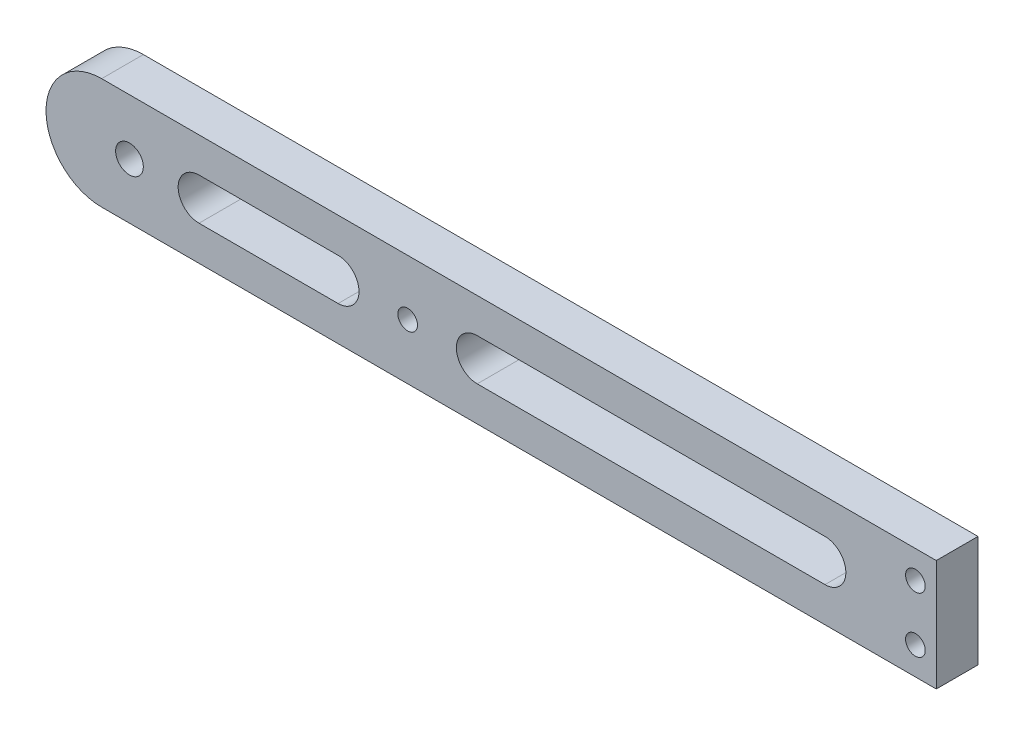
SolidWorks part; units mm, degrees
material "6061-T6 (SS)"
ref_plane "Front Plane" through (0, 0, 0) normal (0, 0, 1) x (1, 0, 0)
ref_plane "Top Plane" through (0, 0, 0) normal (0, 1, 0) x (1, 0, 0)
ref_plane "Right Plane" through (0, 0, 0) normal (1, 0, 0) x (0, 0, -1)
sketch "Sketch1" plane through (0, 0, 0) normal (0, 0, 1) x (1, 0, 0)
  line L1 (0, 0) -> (-203.2, 0)
  line L2 (0, 0) -> (0, 25.4)
  line L3 (0, 25.4) -> (-203.2, 25.4)
  line L4 (-203.2, 0) -> (-203.2, 25.4)
  dimension "D1" = 25.4
  dimension "D2" = 203.2
extrude "Boss-Extrude1" add sketch "Sketch1" along normal blind 9.525
sketch "Sketch2" plane through (0, 0, 9.525) normal (0, 0, 1) x (1, 0, 0)
  line L0 (-4.7625, 6.35) -> (-4.7625, 19.05)
  line L1 (-4.7625, 19.05) -> (-4.7625, 25.4)
  line L2 (0, 25.4) -> (-203.2, 25.4) construction
  line L3 (-4.7625, 6.35) -> (-4.7625, 0)
  line L4 (-203.2, 0) -> (0, 0) construction
  line L5 (0, 0) -> (0, 25.4) construction
  dimension "D1" = 4.7625
  dimension "D2" = 12.7
hole_wizard "#8 Clearance Hole1" positions "Sketch3" profile "Sketch4" hole size "#8" standard "ANSI Inch"
sketch "Sketch3" plane through (0, 0, 9.525) normal (0, 0, 1) x (1, 0, 0)
  point P0 (-4.7625, 6.35)
  point P3 (-4.7625, 19.05)
sketch "Sketch4" plane through (-4.7625, 6.35, 9.525) normal (1, 0, 0) x (0, -1, 0)
  line L0 (0, 0) -> (0, 26.7507)
  line L1 (0, 26.7507) -> (2.2479, 25.4)
  line L2 (2.2479, 25.4) -> (2.2479, 0)
  line L5 (2.2479, 0) -> (0, 0)
  line L10 (0, 26.7507) -> (-2.2479, 25.4) construction
  line L11 (0, -6.35) -> (0, 107.95) construction
  dimension "Hole Dia." = 4.4958
  dimension "Hole Depth" = 25.4
  dimension "Drill Angle" = 118
sketch "Sketch5" plane through (0, 0, 9.525) normal (0, 0, 1) x (1, 0, 0)
  line L0 (-203.2, 12.7) -> (-116.7098, 12.7) construction
  line L1 (-203.2, 25.4) -> (-203.2, 0) construction
  circle A0 centre (-184.15, 12.7) radius 3.1623
  point P4 (-184.15, 12.7)
  dimension "D2" = 6.3246
  dimension "D1" = 19.05
extrude "Cut-Extrude1" cut sketch "Sketch5" against normal blind 9.525 contours A0
hole_wizard "#8 Clearance Hole2" positions "Sketch8" profile "Sketch9" hole size "#8" standard "ANSI Inch"
sketch "Sketch8" plane through (0, 0, 9.525) normal (0, 0, 1) x (1, 0, 0)
  line L0 (-184.15, 12.7) -> (-120.65, 12.7)
  point P2 (-120.65, 12.7)
  dimension "D1" = 63.5
sketch "Sketch9" plane through (-120.65, 12.7, 9.525) normal (1, 0, 0) x (0, -1, 0)
  line L0 (0, 0) -> (0, 20.4007)
  line L1 (0, 20.4007) -> (2.2479, 19.05)
  line L2 (2.2479, 19.05) -> (2.2479, 0)
  line L5 (2.2479, 0) -> (0, 0)
  line L10 (0, 20.4007) -> (-2.2479, 19.05) construction
  line L11 (0, -6.35) -> (0, 107.95) construction
  dimension "Hole Dia." = 4.4958
  dimension "Hole Depth" = 19.05
  dimension "Drill Angle" = 118
sketch "Sketch10" plane through (0, 0, 9.525) normal (0, 0, 1) x (1, 0, 0)
  line L0 (-203.2, 0) -> (0, 0) construction
  line L1 (-203.2, 25.4) -> (-190.5, 25.4)
  line L2 (-203.2, 25.4) -> (-203.2, 0)
  line L3 (-203.2, 0) -> (-177.8, 0)
  arc A0 (-190.5, 0) -> (-190.5, 25.4) centre (-190.5, 12.7) cw
  point P12 (-203.2, 12.7)
  line M8 (0, 25.4) -> (-203.2, 25.4)
  line M9 (-203.2, 25.4) -> (-203.2, 0)
  line M10 (-203.2, 0) -> (0, 0)
extrude "Cut-Extrude2" cut sketch "Sketch10" against normal through all contours A0 M9 M8 | A0 L2 M10
sketch "Sketch11" plane through (0, 0, 0) normal (0, 0, -1) x (-1, 0, 0)
  line L0 (25.4, 12.7) -> (104.775, 12.7) construction
  line L1 (25.4, 17.4625) -> (104.775, 17.4625)
  line L2 (25.4, 7.9375) -> (104.775, 7.9375)
  line L3 (136.525, 12.7) -> (168.275, 12.7) construction
  line L4 (136.525, 17.4625) -> (168.275, 17.4625)
  line L5 (136.525, 7.9375) -> (168.275, 7.9375)
  line L6 (0, 0) -> (0, 25.4) construction
  arc A0 (25.4, 17.4625) -> (25.4, 7.9375) centre (25.4, 12.7) ccw
  arc A1 (104.775, 7.9375) -> (104.775, 17.4625) centre (104.775, 12.7) ccw
  arc A2 (136.525, 17.4625) -> (136.525, 7.9375) centre (136.525, 12.7) ccw
  arc A3 (168.275, 7.9375) -> (168.275, 17.4625) centre (168.275, 12.7) ccw
  circle A4 centre (120.65, 12.7) radius 2.2479 construction
  circle A5 centre (184.15, 12.7) radius 3.1623 construction
  point P2 (65.0875, 12.7)
  point P7 (152.4, 12.7)
  point P16 (0, 12.7)
  point P17 (131.8508, 15.9948)
  point P18 (83.5384, 12.7)
  point P19 (97.7306, 12.7)
  dimension "D1" = 9.525
  dimension "D5" = 15.875
  dimension "D2" = 25.4
  dimension "D3" = 15.875
  dimension "D4" = 15.875
extrude "Cut-Extrude3" cut sketch "Sketch11" against normal through all
